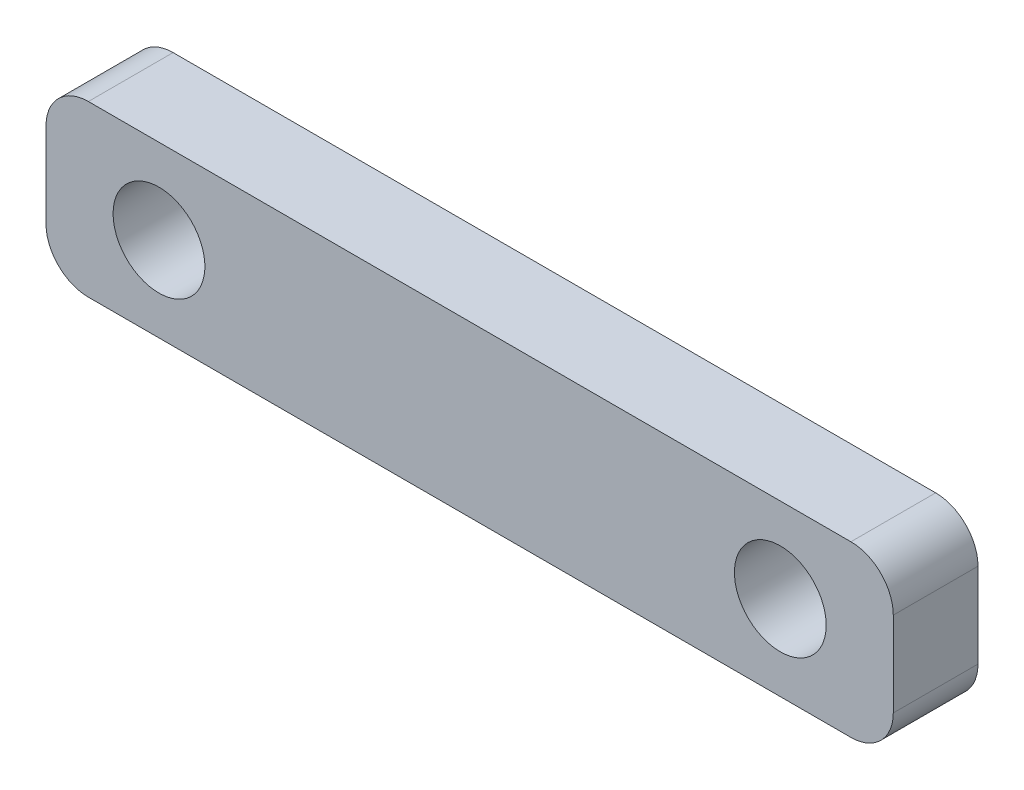
SolidWorks part; units mm, degrees
ref_plane "Plane1" through (0, 0, 0) normal (0, 0, 1) x (1, 0, 0)
ref_plane "Plane2" through (0, 0, 0) normal (0, 1, 0) x (1, 0, 0)
ref_plane "Plane3" through (0, 0, 0) normal (1, 0, 0) x (0, 0, -1)
sketch "Sketch1" plane through (0, 0, 0) normal (0, 0, 1) x (1, 0, 0)
  line L0 (-27, -6) -> (27, -6)
  line L1 (-30, -3) -> (-30, 3)
  line L2 (27, 6) -> (-27, 6)
  line L3 (30, 3) -> (30, -3)
  line L4 (0, -6) -> (0, 6) construction
  line L5 (-30, 0) -> (30, 0) construction
  circle A0 centre (22, 0) radius 3.25
  circle A1 centre (-22, 0) radius 3.25
  arc A2 (-27, 6) -> (-30, 3) centre (-27, 3) ccw
  arc A3 (30, 3) -> (27, 6) centre (27, 3) ccw
  arc A4 (27, -6) -> (30, -3) centre (27, -3) ccw
  arc A5 (-30, -3) -> (-27, -6) centre (-27, -3) ccw
  point P16 (-30, 6)
  point P19 (30, 6)
  point P22 (30, -6)
  dimension "D3" = 44
  dimension "D4" = 6.5
  dimension "D5" = 3
  dimension "D1" = 60
  dimension "D2" = 12
  dimension "D6" = 8
  dimension "D7" = 6
extrude "Base-Extrude" add sketch "Sketch1" along normal blind 6
